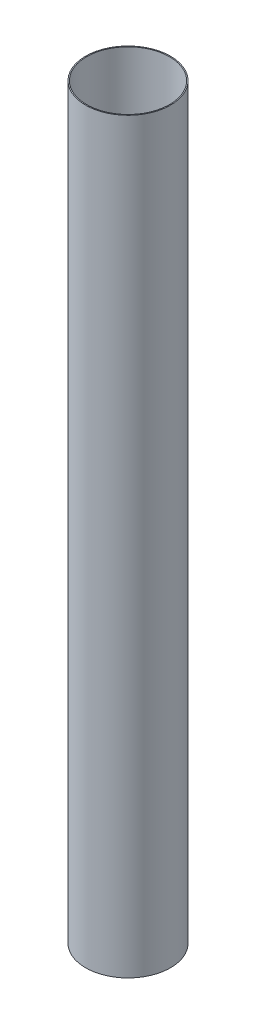
SolidWorks part; units mm, degrees
ref_plane "Front Plane" through (0, 0, 0) normal (0, 0, 1) x (1, 0, 0)
ref_plane "Top Plane" through (0, 0, 0) normal (0, 1, 0) x (1, 0, 0)
ref_plane "Right Plane" through (0, 0, 0) normal (1, 0, 0) x (0, 0, -1)
sketch "Sketch1" plane through (0, 0, 0) normal (0, 0, 1) x (1, 0, 0)
  line L1 (19.0373, 0) -> (19.4945, 0)
  line L2 (19.0373, 0) -> (19.0373, 342.9)
  line L3 (19.0373, 342.9) -> (19.4945, 342.9)
  line L4 (19.4945, 0) -> (19.4945, 342.9)
  dimension "D1" = 19.4945
  dimension "D2" = 0.4572
  dimension "D3" = 342.9
  dimension "D4" = 0
ref_axis "Axis1" through (0, -13.97, 0) along (0, 1, 0)
revolve "Revolve1" add sketch "Sketch1" angle 360 about axis through (0, -13.97, 0) along (0, 1, 0)
